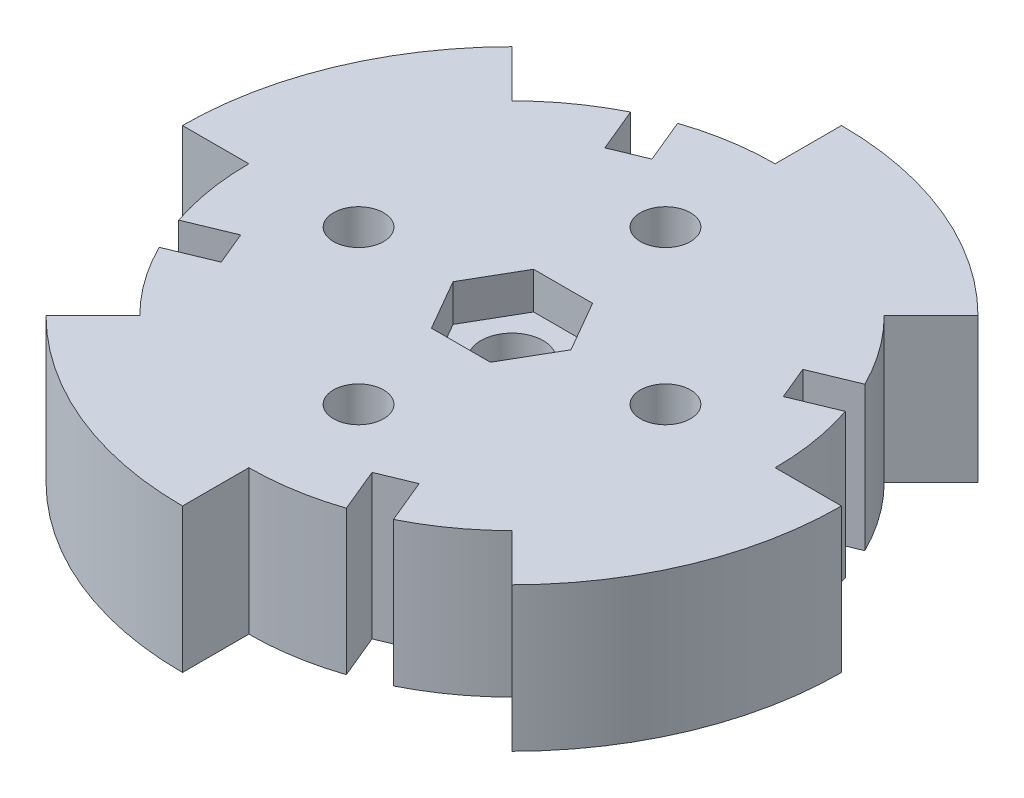
SolidWorks part; units mm, degrees
ref_plane "Front Plane" through (0, 0, 0) normal (0, 0, 1) x (1, 0, 0)
ref_plane "Top Plane" through (0, 0, 0) normal (0, 1, 0) x (1, 0, 0)
ref_plane "Right Plane" through (0, 0, 0) normal (1, 0, 0) x (0, 0, -1)
sketch "Sketch2" plane through (0, 0, 0) normal (0, 1, 0) x (1, 0, 0)
  circle A0 centre (0, 0) radius 27.42
  dimension "D1" = 54.84
extrude "Boss-Extrude1" add sketch "Sketch2" along normal blind 12
sketch "Sketch1" plane through (0, 0, 0) normal (0, 1, 0) x (1, 0, 0)
  line L0 (0, 21.9) -> (0, 27.42)
  line L1 (0, -21.9) -> (0, -27.42)
  line L2 (21.9, 0) -> (27.42, 0)
  line L3 (-21.9, 0) -> (-27.42, 0)
  line L4 (-15.4856, -15.4856) -> (-19.3889, -19.3889)
  line L5 (15.4856, -15.4856) -> (19.3889, -19.3889)
  line L6 (15.4856, 15.4856) -> (19.3889, 19.3889)
  line L7 (-15.4856, 15.4856) -> (-19.3889, 19.3889)
  arc A0 (27.42, 0) -> (19.3889, 19.3889) centre (0, 0) ccw
  arc A1 (21.9, 0) -> (15.4856, 15.4856) centre (0, 0) ccw
  arc A2 (0, 21.9) -> (-15.4856, 15.4856) centre (0, 0) ccw
  arc A3 (0, 27.42) -> (-19.3889, 19.3889) centre (0, 0) ccw
  arc A4 (-21.9, 0) -> (-15.4856, -15.4856) centre (0, 0) ccw
  arc A5 (-27.42, 0) -> (-19.3889, -19.3889) centre (0, 0) ccw
  arc A6 (0, -21.9) -> (15.4856, -15.4856) centre (0, 0) ccw
  arc A7 (0, -27.42) -> (19.3889, -19.3889) centre (0, 0) ccw
  dimension "D1" = 54.84
  dimension "D2" = 43.8
  dimension "D3" = 45
  dimension "D4" = 45
extrude "Cut-Extrude1" cut sketch "Sketch1" along normal through all
sketch "Sketch3" plane through (0, 12, 0) normal (0, 1, 0) x (1, 0, 0)
  circle A0 centre (12.77, 0) radius 2.085
  point P2 (0, 0)
  dimension "D1" = 4.17
  dimension "D2" = 12.77
extrude "Cut-Extrude2" cut sketch "Sketch3" against normal through all
pattern_circular "CirPattern1" count 4 over 360 about axis through (0, 0, 0) along (0, 1, 0) of "Cut-Extrude2"
sketch "Sketch5" plane through (0, 12, 0) normal (0, 1, 0) x (1, 0, 0)
  line L0 (-5.4642, 17.1115) -> (-7.4136, 21.8177)
  line L1 (-6.85, 16.5374) -> (-5.4642, 17.1115)
  line L2 (-6.85, 16.5374) -> (-8.2359, 15.9634)
  line L3 (-7.4136, 21.8177) -> (-10.1852, 20.6697)
  line L4 (-10.1852, 20.6697) -> (-8.2359, 15.9634)
  line L5 (-8.3808, 20.233) -> (-6.85, 16.5374) construction
  line L6 (-8.3808, 20.233) -> (-6.9949, 20.807) construction
  arc A1 (0, 21.9) -> (-15.4856, 15.4856) centre (0, 0) ccw construction
  dimension "D1" = 3
  dimension "D2" = 4
extrude "Cut-Extrude4" cut sketch "Sketch5" against normal through all
pattern_circular "CirPattern2" count 4 over 360 about axis through (0, 0, 0) along (0, 1, 0) of "Cut-Extrude4"
hole_wizard "#6 (0.204) Diameter Hole1" positions "Sketch7" profile "Sketch6" hole size "#6" standard "ANSI Inch"
sketch "Sketch7" plane through (0, 12, 0) normal (0, 1, 0) x (1, 0, 0)
  point P0 (0, 0)
sketch "Sketch6" plane through (0, 12, 0) normal (1, 0, 0) x (0, 0, 1)
  line L0 (0, 0) -> (0, 13.5567)
  line L1 (0, 13.5567) -> (2.5908, 12)
  line L2 (2.5908, 12) -> (2.5908, 0)
  line L5 (2.5908, 0) -> (0, 0)
  line L10 (0, 13.5567) -> (-2.5908, 12) construction
  line L11 (0, -6.35) -> (0, 107.95) construction
  dimension "Hole Dia." = 5.1816
  dimension "Hole Depth" = 12
  dimension "Drill Angle" = 118
sketch "Sketch8" plane through (0, 12, 0) normal (0, 1, 0) x (1, 0, 0)
  line L1 (2.4537, -4.25) -> (4.9075, 0)
  line L2 (4.9075, 0) -> (2.4537, 4.25)
  line L3 (2.4537, 4.25) -> (-2.4537, 4.25)
  line L4 (-2.4537, 4.25) -> (-4.9075, 0)
  line L5 (-4.9075, 0) -> (-2.4537, -4.25)
  line L6 (-2.4537, -4.25) -> (2.4537, -4.25)
  circle A0 centre (0, 0) radius 4.25 construction
  dimension "D1" = 8.5
extrude "Cut-Extrude5" cut sketch "Sketch8" against normal blind 3.08
